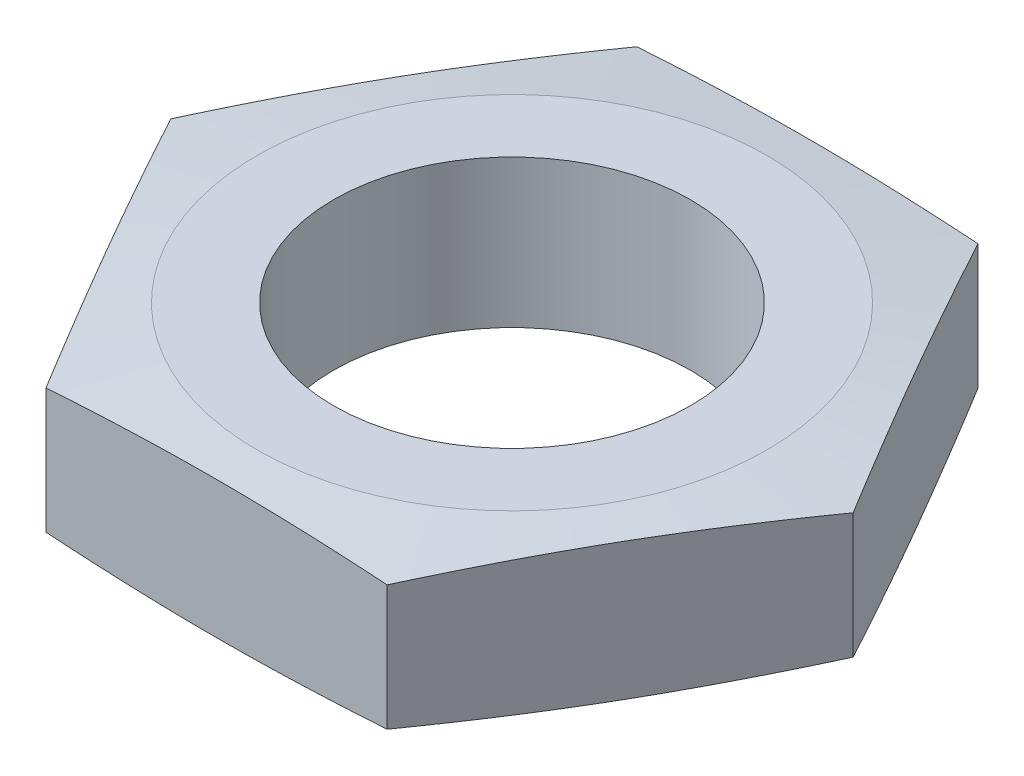
SolidWorks part; units mm, degrees
material "AISI Type 316L stainless steel"
ref_plane "Front" through (0, 0, 0) normal (0, 0, 1) x (1, 0, 0)
ref_plane "Top" through (0, 0, 0) normal (0, 1, 0) x (1, 0, 0)
ref_plane "Right" through (0, 0, 0) normal (1, 0, 0) x (0, 0, -1)
sketch "Sketch1" plane through (0, 0, 0) normal (0, 1, 0) x (1, 0, 0)
  line L0 (0, -50) -> (0, 50) construction
  line L1 (6.9282, 12) -> (-6.9282, 12)
  line L2 (-6.9282, 12) -> (-13.8564, 0)
  line L3 (-13.8564, 0) -> (-6.9282, -12)
  line L4 (-6.9282, -12) -> (6.9282, -12)
  line L5 (6.9282, -12) -> (13.8564, 0)
  line L6 (13.8564, 0) -> (6.9282, 12)
  circle A0 centre (0, 0) radius 12 construction
  point P1 (0, 12)
  dimension "D1" = 24
extrude "Boss-Extrude1" add sketch "Sketch1" along normal blind 6
sketch "Sketch2" plane through (0, 0, 0) normal (0, 0, 1) x (1, 0, 0)
  line L0 (0, 0) -> (0, 6) construction
  line L2 (-6.9282, 6) -> (6.9282, 6) construction
  line L3 (-13.8564, 0) -> (-10.3564, 0)
  line L4 (-13.8564, 0) -> (-6.9282, 0) construction
  line L5 (-10.3564, 0) -> (-13.8564, 0.4608)
  line L6 (-13.8564, 6) -> (-13.8564, 0) construction
  line L7 (-13.8564, 0.4608) -> (-13.8564, 0)
  line L8 (-13.8564, 6) -> (-10.3564, 6)
  line L9 (-13.8564, 6) -> (-6.9282, 6) construction
  line L10 (-10.3564, 6) -> (-13.8564, 5.5392)
  line L11 (-13.8564, 5.5392) -> (-13.8564, 6)
  dimension "D1" = 6
  dimension "D2" = 3.5
  dimension "D3" = 7.5
  dimension "D4" = 3.5
  dimension "D5" = 7.5
revolve "Cut-Revolve1" cut sketch "Sketch2" angle 360 about L0
hole_wizard "M16x1.5 Tapped Hole1" positions "Sketch4" profile "Sketch3" tap size "M16x1.5" standard "ANSI Metric"
sketch "Sketch4" plane through (0, 6, 0) normal (0, 1, 0) x (1, 0, 0)
  point P0 (0, 0)
sketch "Sketch3" plane through (0, 6, 0) normal (1, 0, 0) x (0, 0, 1)
  line L0 (0, 0) -> (0, 43.8562)
  line L1 (0, 43.8562) -> (7.25, 39.5)
  line L2 (7.25, 39.5) -> (7.25, 0)
  line L5 (7.25, 0) -> (0, 0)
  line L10 (0, 43.8562) -> (-7.25, 39.5) construction
  line L11 (0, -6.35) -> (0, 107.95) construction
  dimension "Tap Drill Dia." = 14.5
  dimension "Tap Drill Depth" = 39.5
  dimension "Drill Angle" = 118
cosmetic thread "Hole Thread1" parameters "D1"=6, "D2"=16
